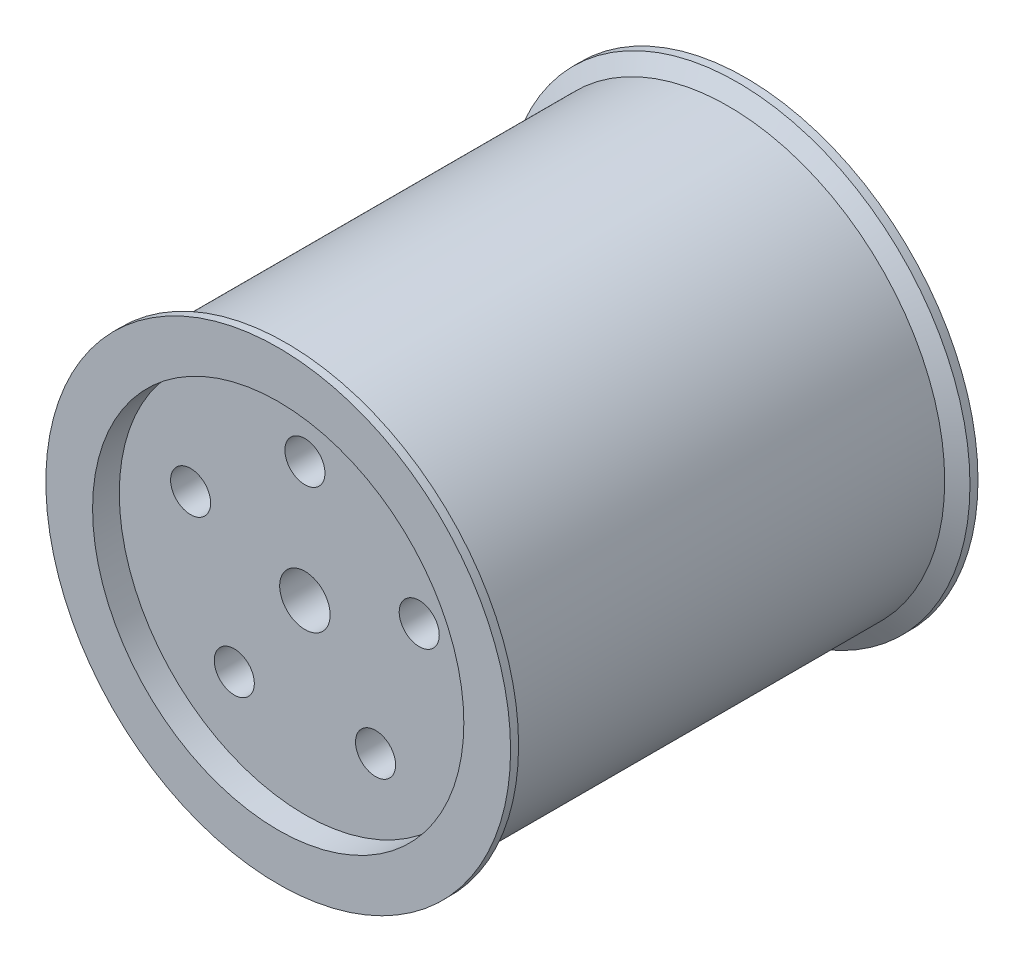
SolidWorks part; units mm, degrees
ref_plane "Front Plane" through (0, 0, 0) normal (0, 0, 1) x (1, 0, 0)
ref_plane "Top Plane" through (0, 0, 0) normal (0, 1, 0) x (1, 0, 0)
ref_plane "Right Plane" through (0, 0, 0) normal (1, 0, 0) x (0, 0, -1)
sketch "Sketch1" plane through (0, 0, 0) normal (0, 0, 1) x (1, 0, 0)
  circle A0 centre (0, 0) radius 87
  dimension "D1" = 174
extrude "Boss-Extrude1" add sketch "Sketch1" along normal mid plane 175
sketch "Sketch2" plane through (0, 0, 87.5) normal (0, 0, 1) x (1, 0, 0)
  circle A0 centre (0, 0) radius 9.4488
  dimension "D1" = 18.8976
extrude "Cut-Extrude1" cut sketch "Sketch2" against normal through all both and the other way through all
sketch "Sketch3" plane through (0, 0, 87.5) normal (0, 0, 1) x (1, 0, 0)
  circle A0 centre (0, 0) radius 69.5
  circle A1 centre (0, 0) radius 87 construction
  dimension "D1" = 17.5
extrude "Cut-Extrude2" cut sketch "Sketch3" against normal blind 10
mirror "Mirror1" about plane through (0, 0, 0) normal (0, 0, 1) of "Cut-Extrude2"
sketch "Sketch4" plane through (0, 0, 77.5) normal (0, 0, 1) x (1, 0, 0)
  circle A0 centre (0, 0) radius 9.4488 construction
  circle A1 centre (0, 0) radius 9.4488
  circle A2 centre (0, 0) radius 11
  dimension "D1" = 22
sketch "Sketch5" plane through (0, 0, 0) normal (0, 1, 0) x (1, 0, 0)
  line L0 (87, 84.5) -> (81, 81.0359)
  line L1 (87, -87.5) -> (87, 87.5) construction
  line L2 (81, 81.0359) -> (81, -81.0359)
  line L3 (81, -81.0359) -> (87, -84.5)
  line L4 (87, 84.5) -> (87, -84.5)
  line L5 (0, 0) -> (0, 24.1674) construction
  dimension "D1" = 3
  dimension "D2" = 3
  dimension "D3" = 60
  dimension "D4" = 60
  dimension "D5" = 6
revolve "Cut-Revolve1" cut sketch "Sketch5" angle 360 about L5
sketch "Sketch7" plane through (0, 0, 77.5) normal (0, 0, 1) x (1, 0, 0)
  circle A0 centre (0, 45) radius 7.5
  dimension "D1" = 15
  dimension "D2" = 45
extrude "Cut-Extrude3" cut sketch "Sketch7" against normal through all
pattern_circular "CirPattern1" count 5 over 360 about axis through (0, 0, 0) along (0, 0, 1) of "Cut-Extrude3"
sketch "Sketch8" plane through (0, 0, 77.5) normal (0, 0, 1) x (1, 0, 0)
  circle A0 centre (0, 0) radius 19.05
  dimension "D1" = 38.1
